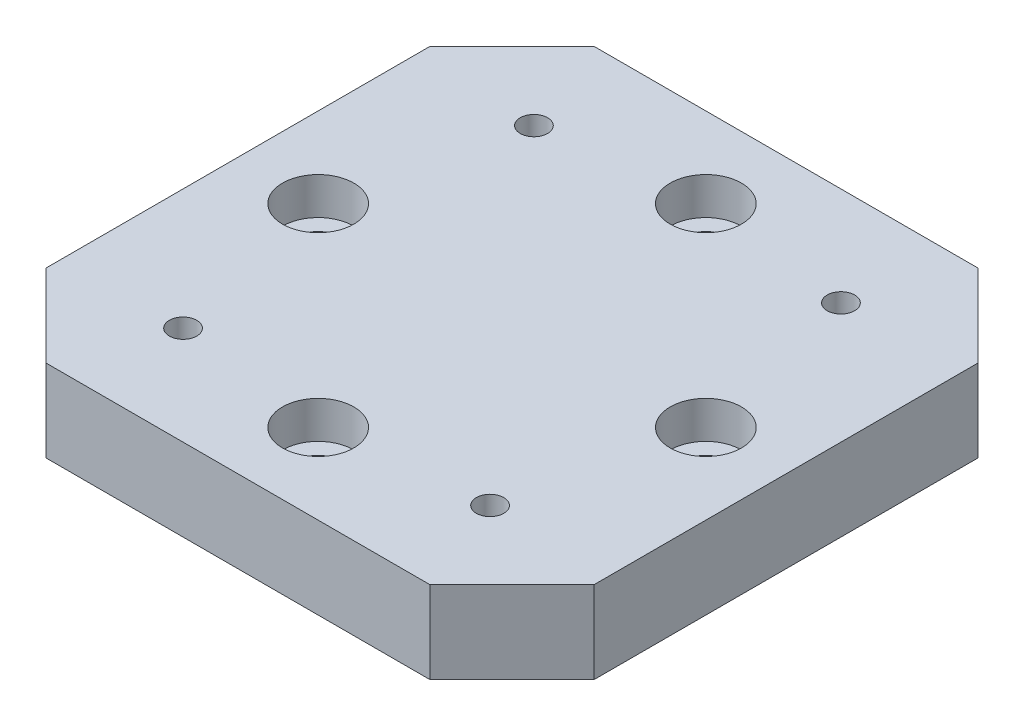
SolidWorks part; units mm, degrees
ref_plane "Front Plane" through (0, 0, 0) normal (0, 0, 1) x (1, 0, 0)
ref_plane "Top Plane" through (0, 0, 0) normal (0, 1, 0) x (1, 0, 0)
ref_plane "Right Plane" through (0, 0, 0) normal (1, 0, 0) x (0, 0, -1)
sketch "Sketch1" plane through (0, 0, 0) normal (0, 1, 0) x (1, 0, 0)
  line L1 (-25, -25) -> (25, -25)
  line L2 (-25, -25) -> (-25, 25)
  line L3 (-25, 25) -> (25, 25)
  line L4 (25, -25) -> (25, 25)
  line L5 (-25, -25) -> (25, 25) construction
  line L6 (-25, 25) -> (25, -25) construction
  point P0 (0, 0)
  dimension "D1" = 50
extrude "Boss-Extrude1" add sketch "Sketch1" along normal blind 7.5
hole_wizard "M3 Tapped Hole1" positions "Sketch2" profile "Sketch3" tap size "M3" standard "DIN" end condition up to next
sketch "Sketch2" plane through (0, 7.5, 0) normal (0, 1, 0) x (1, 0, 0)
  line L1 (-14, -16) -> (14, -16)
  line L2 (-14, -16) -> (-14, 16)
  line L3 (-14, 16) -> (14, 16)
  line L4 (14, -16) -> (14, 16)
  line L5 (-14, -16) -> (14, 16) construction
  line L6 (-14, 16) -> (14, -16) construction
  point P0 (-14, -16)
  point P2 (-14, 16)
  point P4 (14, 16)
  point P6 (14, -16)
  dimension "D1" = 32
  dimension "D2" = 28
sketch "Sketch3" plane through (-14, 7.5, 16) normal (1, 0, 0) x (0, 0, 1)
  line L0 (0, 0) -> (0, 7.5)
  line L1 (0, 7.5) -> (1.25, 7.5)
  line L2 (1.25, 7.5) -> (1.25, 0)
  line L5 (1.25, 0) -> (0, 0)
  line L11 (0, -6.35) -> (0, 107.95) construction
  dimension "Thru Tap Drill Dia." = 2.5
  dimension "Thru Tap Drill Depth" = 7.5
cosmetic thread "Hole Thread1"
cosmetic thread "Hole Thread2"
cosmetic thread "Hole Thread3"
cosmetic thread "Hole Thread4"
hole_wizard "CBORE for M3 Hex Socket Head Cap Screw1" positions "Sketch4" profile "Sketch5" counterbore size "M3" standard "DIN" end condition up to next
sketch "Sketch4" plane through (0, 7.5, 0) normal (0, 1, 0) x (1, 0, 0)
  line L0 (0, 17.6777) -> (0, -17.6777) construction
  line L2 (-17.6777, 0) -> (17.6777, 0) construction
  point P0 (0, 17.6777)
  point P2 (-17.6777, 0)
  point P4 (17.6777, 0)
  point P6 (0, -17.6777)
  dimension "D1" = 25
sketch "Sketch5" plane through (0, 7.5, -17.6777) normal (1, 0, 0) x (0, 0, 1)
  line L0 (0, 0) -> (0, 7.5)
  line L1 (0, 7.5) -> (1.7, 7.5)
  line L3 (1.7, 7.5) -> (1.7, 3.4)
  line L4 (1.7, 3.4) -> (3.25, 3.4)
  line L5 (3.25, 3.4) -> (3.25, 0)
  line L7 (3.25, 0) -> (0, 0)
  line L11 (0, -6.35) -> (0, 107.95) construction
  dimension "Thru Hole Dia." = 3.4
  dimension "Thru Hole Depth" = 7.5
  dimension "C'Bore Dia." = 6.5
  dimension "C'Bore Depth" = 3.4
chamfer "Chamfer1" distance 7.5 angle 45 4 edges at (25, 3.75, 25) (-25, 3.75, 25) (25, 3.75, -25) (-25, 3.75, -25)
